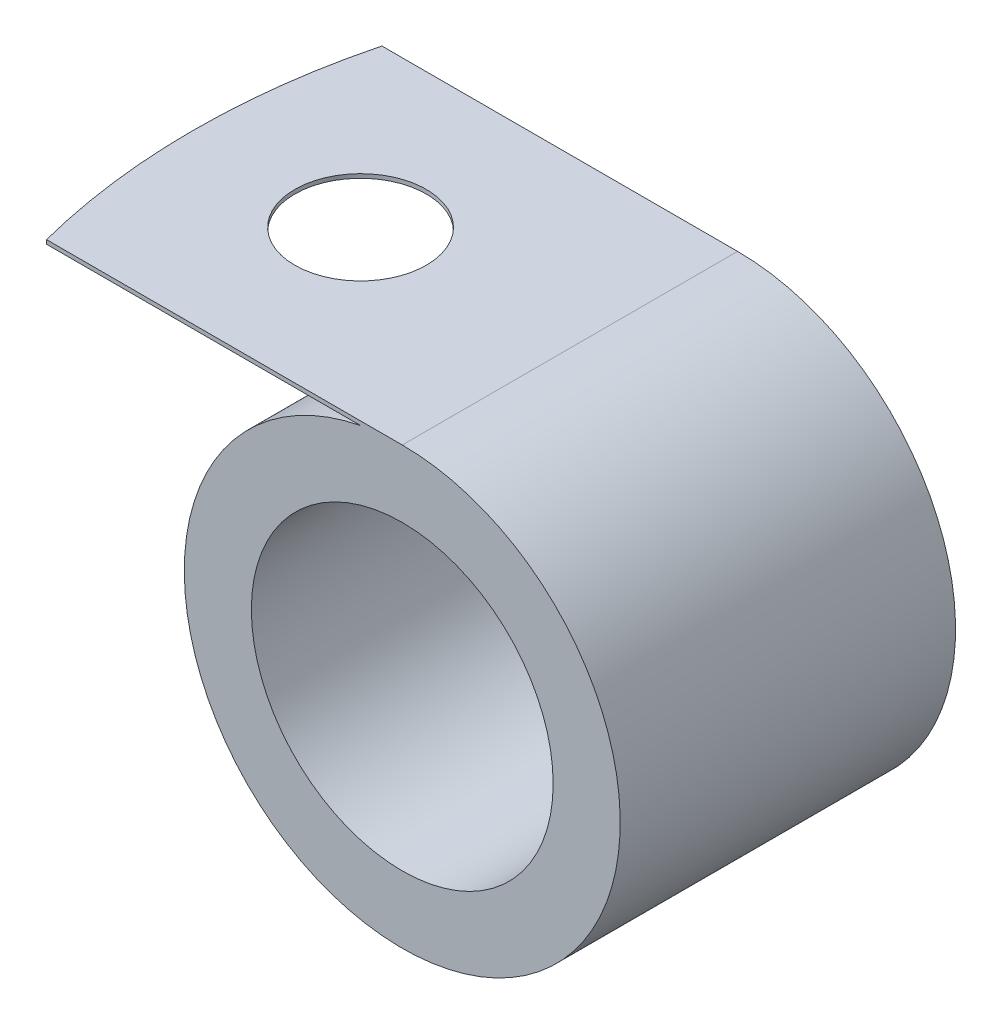
SolidWorks part; units mm, degrees
ref_plane "Front Plane" through (0, 0, 0) normal (0, 0, 1) x (1, 0, 0)
ref_plane "Top Plane" through (0, 0, 0) normal (0, 1, 0) x (1, 0, 0)
ref_plane "Right Plane" through (0, 0, 0) normal (1, 0, 0) x (0, 0, -1)
sketch "Sketch1" plane through (0, 0, 0) normal (0, 0, 1) x (1, 0, 0)
  line L0 (0, 8.255) -> (-14.2789, 8.255)
  line L1 (-14.2789, 8.255) -> (-14.2789, 8.1026)
  line L2 (-14.2789, 8.1026) -> (-1.5789, 8.1026)
  circle A0 centre (0, 0) radius 5.715
  circle A1 centre (0, 0) radius 8.255
  dimension "D1" = 16.51
  dimension "D2" = 11.43
  dimension "D3" = 0.1524
  dimension "D4" = 12.7
extrude "Boss-Extrude1" add sketch "Sketch1" along normal mid plane 12.7 contours A1 A0 | A1 L0 L1 L2
sketch "Sketch5" plane through (0, 8.255, 0) normal (0, 1, 0) x (1, 0, 0)
  line L0 (0, 6.35) -> (-14.2789, 6.35) construction
  line L1 (0, -6.35) -> (-14.2789, -6.35) construction
  line L2 (-14.2789, -6.35) -> (-14.2789, 6.35) construction
  line L7 (0, 6.35) -> (-14.2789, 6.35)
  line L8 (-14.2789, 6.35) -> (-14.2789, -6.35)
  line L9 (-14.2789, -6.35) -> (0, -6.35)
  line L10 (0, -6.35) -> (0, 6.35)
  line L11 (0, 6.35) -> (-14.2789, 6.35)
  line L12 (-14.2789, 6.35) -> (-14.2789, -6.35)
  line L13 (-14.2789, -6.35) -> (0, -6.35)
  line L14 (0, -6.35) -> (0, 6.35)
  arc A0 (-13.4723, 6.35) -> (-13.4723, -6.35) centre (11.1211, 0) ccw
  circle A1 centre (-7.9289, 0) radius 2.4892
  line M6 (-14.2789, 6.35) -> (-14.2789, -6.35)
  line M7 (-14.2789, -6.35) -> (0, -6.35)
  dimension "D1" = 25.4
  dimension "D2" = 4.9784
  dimension "D3" = 6.35
  dimension "D4" = 0
extrude "Cut-Extrude1" cut sketch "Sketch5" against normal up to next contours A0 L11 M6 | A0 L12 M7 | A1
